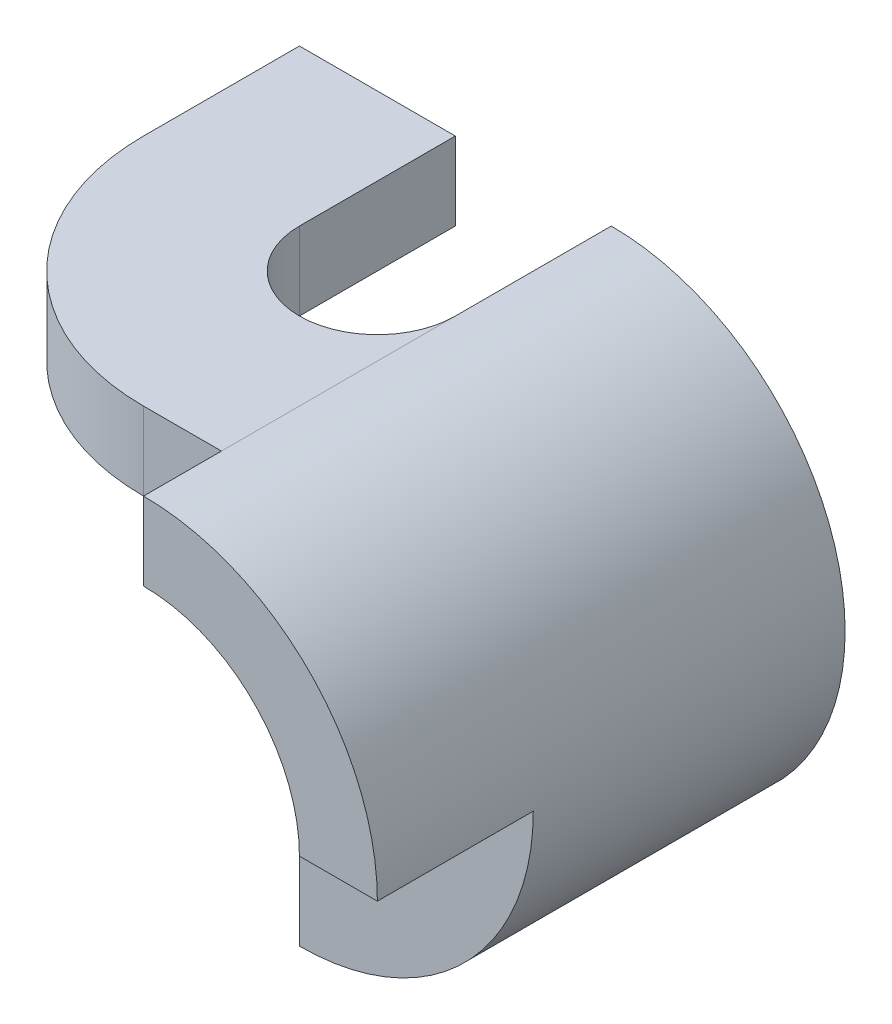
SolidWorks part; units mm, degrees
ref_plane "Front Plane" through (0, 0, 0) normal (0, 0, 1) x (1, 0, 0)
ref_plane "Top Plane" through (0, 0, 0) normal (0, 1, 0) x (1, 0, 0)
ref_plane "Right Plane" through (0, 0, 0) normal (1, 0, 0) x (0, 0, -1)
sketch "Sketch1" plane through (0, 0, 0) normal (0, 0, 1) x (1, 0, 0)
  line L0 (0, 2) -> (-4, 2)
  line L1 (-4, 2) -> (-4, 3)
  line L2 (-4, 3) -> (0, 3)
  line L3 (0, -2) -> (-1, -2)
  line L4 (-1, -2) -> (-1, -3)
  line L5 (-1, -3) -> (0, -3)
  arc A0 (0, 2) -> (0, -2) centre (0, 0) cw
  arc A1 (0, 3) -> (0, -3) centre (0, 0) cw
  dimension "D1" = 2
  dimension "D2" = 3
  dimension "D3" = 1
  dimension "D4" = 4
  dimension "D5" = 1
  dimension "D6" = 1
extrude "Boss-Extrude1" add sketch "Sketch1" along normal blind 6
sketch "Sketch2" plane through (0, 0, 6) normal (0, 0, 1) x (1, 0, 0)
  line L0 (3, 0) -> (2, 0)
  line L1 (0, -2) -> (0, -3)
  arc A0 (0, -3) -> (0, 3) centre (0, 0) ccw construction
  arc A1 (0, -2) -> (0, 2) centre (0, 0) ccw construction
  arc A2 (3, 0) -> (0, -3) centre (0, 0) cw
  arc A3 (2, 0) -> (0, -2) centre (0, 0) cw
extrude "Cut-Extrude1" cut sketch "Sketch2" against normal blind 2
sketch "Sketch3" plane through (0, -3, 0) normal (0, -1, 0) x (1, 0, 0)
  line L0 (0, 4) -> (-1, 2)
  line L1 (-1, 6) -> (-1, 0) construction
  line L2 (-1, 2) -> (-1, 6)
  line L3 (-1, 6) -> (0, 6)
  line L4 (0, 6) -> (0, 4)
  dimension "D1" = 2
extrude "Cut-Extrude2" cut sketch "Sketch3" against normal blind 2
sketch "Sketch4" plane through (0, 2, 0) normal (0, -1, 0) x (1, 0, 0)
  line L0 (-4, 0) -> (-4, 2)
  line L1 (-4, 6) -> (-4, 0) construction
  line L3 (0, 5) -> (-1, 5)
  line L4 (0, 6) -> (0, 0) construction
  line L5 (-4, 6) -> (0, 6) construction
  line L6 (-4, 2) -> (-4, 6)
  line L7 (-4, 6) -> (0, 6)
  line L8 (0, 6) -> (0, 5)
  arc A0 (-1, 5) -> (-4, 2) centre (-1, 2) ccw
  line M2 (0, 0) -> (0, 6)
  line M3 (0, 6) -> (-4, 6)
  line M4 (-4, 6) -> (-4, 0)
  dimension "D3" = 1
  dimension "D1" = 2
  dimension "D2" = 1
extrude "Cut-Extrude3" cut sketch "Sketch4" against normal blind 2 contours A0 L3 M2 M3 M4
sketch "Sketch5" plane through (0, 3, 0) normal (0, 1, 0) x (1, 0, 0)
  line L0 (-2, 0) -> (-2, -2)
  line L1 (0, 0) -> (-4, 0) construction
  line L2 (0, 0) -> (0, -2)
  line L4 (-4, -2) -> (-4, 0) construction
  line L5 (0, 0) -> (-2, 0)
  arc A0 (-2, -2) -> (0, -2) centre (-1, -2) ccw
  dimension "D1" = 2
  dimension "D2" = 2
  dimension "D3" = 2
  dimension "D4" = 2
extrude "Cut-Extrude4" cut sketch "Sketch5" against normal blind 3
